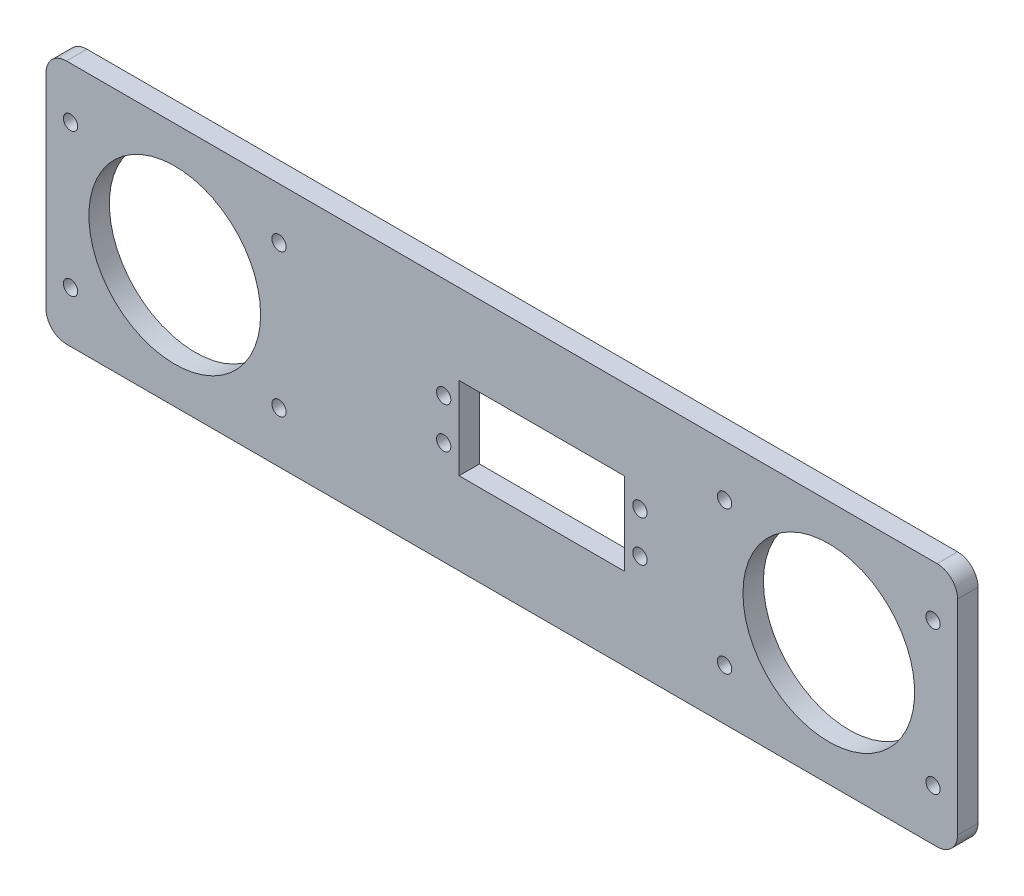
SolidWorks part; units mm, degrees
ref_plane "前视基准面" through (0, 0, 0) normal (0, 0, 1) x (1, 0, 0)
ref_plane "上视基准面" through (0, 0, 0) normal (0, 1, 0) x (1, 0, 0)
ref_plane "右视基准面" through (0, 0, 0) normal (1, 0, 0) x (0, 0, -1)
sketch "草图1" plane through (0, 0, 0) normal (0, 0, 1) x (1, 0, 0)
  line L0 (30.0389, -9.8623) -> (30.0389, 10.3377) construction
  line L1 (106.5, -30) -> (-106.5, -30)
  line L2 (111.5, -25) -> (111.5, 25)
  line L3 (106.5, 30) -> (-106.5, 30)
  line L4 (-111.5, -25) -> (-111.5, 25)
  line L5 (0, 30) -> (0, -30) construction
  line L6 (111.5, 0) -> (-111.5, 0) construction
  line L7 (30.0389, 10.3377) -> (-10.4611, 10.3377) construction
  line L8 (-10.4611, 10.3377) -> (-10.4611, -9.8623) construction
  line L9 (-10.4611, -9.8623) -> (30.0389, -9.8623) construction
  line L10 (30.0389, -9.8623) -> (30.0389, 10.3377)
  line L11 (30.0389, 10.3377) -> (-10.4611, 10.3377)
  line L12 (-10.4611, 10.3377) -> (-10.4611, -9.8623)
  line L13 (-10.4611, -9.8623) -> (30.0389, -9.8623)
  circle A0 centre (-80, 0) radius 21
  circle A1 centre (80, 0) radius 21
  arc A2 (111.5, 25) -> (106.5, 30) centre (106.5, 25) ccw
  arc A3 (106.5, -30) -> (111.5, -25) centre (106.5, -25) ccw
  arc A4 (-106.5, -30) -> (-111.5, -25) centre (-106.5, -25) cw
  arc A5 (-106.5, 30) -> (-111.5, 25) centre (-106.5, 25) ccw
  circle A6 centre (0, 0) radius 1.75 construction
  circle A7 centre (33.7889, -4.7623) radius 1.75 construction
  circle A8 centre (33.7889, 5.2377) radius 1.75 construction
  circle A9 centre (-14.2111, -4.7623) radius 1.75 construction
  circle A10 centre (-14.2111, 5.2377) radius 1.75 construction
  circle A11 centre (33.7889, -4.7623) radius 1.75
  circle A12 centre (33.7889, 5.2377) radius 1.75
  circle A13 centre (-14.2111, -4.7623) radius 1.75
  circle A14 centre (-14.2111, 5.2377) radius 1.75
  circle A15 centre (-54.5, -17.5) radius 1.75
  circle A16 centre (-105.5, -17.5) radius 1.75
  circle A17 centre (-105.5, 17.5) radius 1.75
  circle A18 centre (-54.5, 17.5) radius 1.75
  circle A19 centre (54.5, -17.5) radius 1.75
  circle A20 centre (54.5, 17.5) radius 1.75
  circle A21 centre (105.5, -17.5) radius 1.75
  circle A22 centre (105.5, 17.5) radius 1.75
  point P0 (0, 0)
  point P13 (111.5, 30)
  point P18 (-111.5, -30)
  point P21 (-111.5, 30)
  dimension "D3" = 42
  dimension "D5" = 5
  dimension "D6" = 3.5
  dimension "D7" = 3.5
  dimension "D8" = 3.5
  dimension "D9" = 3.5
  dimension "D10" = 3.5
  dimension "D1" = 60
  dimension "D2" = 223
  dimension "D4" = 160
extrude "凸台-拉伸1" add sketch "草图1" along normal blind 5
ref_plane "基准面1" through (0, 0, 0) normal (-1, 0, 0) x (0, 0, 1)
